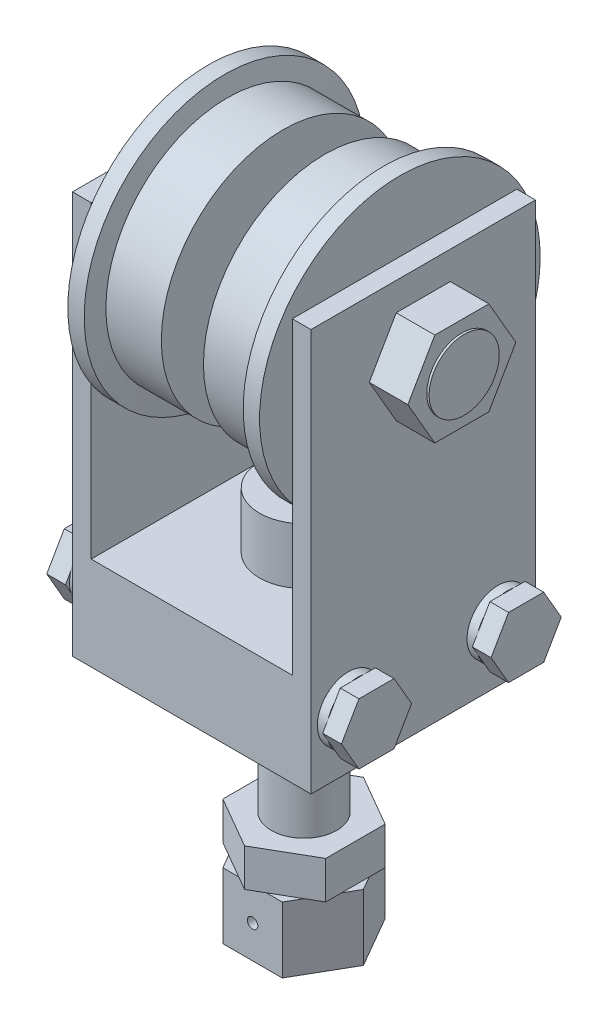
SolidWorks part; units mm, degrees
ref_plane "Front" through (0, 0, 0) normal (0, 0, 1) x (1, 0, 0)
ref_plane "Top" through (0, 0, 0) normal (0, 1, 0) x (1, 0, 0)
ref_plane "Right" through (0, 0, 0) normal (1, 0, 0) x (0, 0, -1)
ref_plane "Z PLANE" through (0, 0, 0) normal (0, 0, 1) x (1, 0, 0)
ref_plane "YOKE BOTTOM" through (0, 0, 0) normal (0, 1, 0) x (-1, 0, 0)
ref_plane "X PLANE" through (0, 0, 0) normal (1, 0, 0) x (0, 0, -1)
sketch "YOKE CROSS SECTION" plane through (0, 0, 0) normal (1, 0, 0) x (0, 0, -1)
  line L0 (0, 0) -> (0, 57.0916) construction
  line L1 (0, 84.8167) -> (0, -84.8167) construction
  line L2 (-76.2, 0) -> (76.2, 0)
  line L3 (69.1602, 0) -> (-69.1602, 0) construction
  line L4 (76.2, 0) -> (76.2, 63.5)
  line L5 (-76.2, 0) -> (-76.2, 63.5)
  line L6 (76.2, 63.5) -> (-76.2, 63.5)
  point P12 (0, 63.5)
  dimension "D1" = 63.5
  dimension "D2" = 152.4
ref_plane "1/2 YOKE LENGTH (A)" through (68.2625, 0, 0) normal (1, 0, 0) x (0, 0, -1)
extrude "YOKE" add sketch "YOKE CROSS SECTION" along normal up to surface (68.2625 mm away) up to plane "1/2 YOKE LENGTH (A)"
sketch "SIDEPLATE PROFILE" plane through (68.2625, 0, 0) normal (1, 0, 0) x (0, 0, -1)
  line L0 (0, 0) -> (0, 74.7424) construction
  line L1 (0, 84.8167) -> (0, -84.8167) construction
  line L2 (-76.2, 0) -> (76.2, 0)
  line L3 (76.2, 0) -> (76.2, 273.05)
  line L4 (-76.2, 0) -> (-76.2, 273.05)
  line L5 (76.2, 273.05) -> (-76.2, 273.05)
  point P11 (0, 273.05)
  dimension "D1" = 273.05
ref_plane "WHEEL HEIGHT" through (0, 222.25, 0) normal (0, 1, 0) x (-1, 0, 0)
ref_plane "SCREW LOCATION X" through (0, 0, 50.8) normal (0, 0, 1) x (1, 0, 0)
ref_plane "SCREW LOCATION Y" through (0, 38.1, 0) normal (0, 1, 0) x (-1, 0, 0)
extrude "SIDEPLATE" add sketch "SIDEPLATE PROFILE" along normal blind 12.7
sketch "WHEEL PIN NUT PROFILE" plane through (80.9625, 0, 0) normal (1, 0, 0) x (0, 0, -1)
  line L0 (0, 84.8167) -> (0, -84.8167) construction
  line L1 (36.6617, 222.25) -> (18.3309, 254)
  line L2 (18.3309, 254) -> (-18.3309, 254)
  line L3 (-18.3309, 254) -> (-36.6617, 222.25)
  line L4 (-36.6617, 222.25) -> (-18.3309, 190.5)
  line L5 (-18.3309, 190.5) -> (18.3309, 190.5)
  line L6 (18.3309, 190.5) -> (36.6617, 222.25)
  line L7 (69.1602, 222.25) -> (-69.1602, 222.25) construction
  circle A0 centre (0, 222.25) radius 31.75 construction
  dimension "D1" = 63.5
extrude "WHEEL PIN NUT" add sketch "WHEEL PIN NUT PROFILE" along normal blind 26.1937
sketch "WHEEL PIN PROJECTION PROFILE" plane through (107.1563, 0, 0) normal (1, 0, 0) x (0, 0, -1)
  line L0 (0, 84.8167) -> (0, -84.8167) construction
  line L1 (69.1602, 222.25) -> (-69.1602, 222.25) construction
  circle A0 centre (0, 222.25) radius 23.8125
  dimension "D1" = 47.625
extrude "WHEEL PIN PROJECTION" add sketch "WHEEL PIN PROJECTION PROFILE" along normal blind 1.5875
sketch "LOCKNUTS PROFILE" plane through (80.9625, 0, 0) normal (1, 0, 0) x (0, 0, -1)
  line L0 (-50.8, 84.8167) -> (-50.8, -84.8167) construction
  line L1 (50, 38.1) -> (-50, 38.1) construction
  circle A0 centre (-50.8, 38.1) radius 21.0947
  dimension "D1" = 42.1894
extrude "LOCKNUTS" add sketch "LOCKNUTS PROFILE" along normal blind 6.35
sketch "SCREWS PROFILE" plane through (87.3125, 0, 0) normal (1, 0, 0) x (0, 0, -1)
  line L0 (50, 38.1) -> (-50, 38.1) construction
  line L1 (-26.9699, 38.1) -> (-38.8849, 58.7375)
  line L2 (-38.8849, 58.7375) -> (-62.7151, 58.7375)
  line L3 (-62.7151, 58.7375) -> (-74.6301, 38.1)
  line L4 (-74.6301, 38.1) -> (-62.7151, 17.4625)
  line L5 (-62.7151, 17.4625) -> (-38.8849, 17.4625)
  line L6 (-38.8849, 17.4625) -> (-26.9699, 38.1)
  line L7 (-50.8, 84.8167) -> (-50.8, -84.8167) construction
  circle A0 centre (-50.8, 38.1) radius 20.6375 construction
  dimension "D1" = 41.275
extrude "SCREWS" add sketch "SCREWS PROFILE" along normal blind 12.7
sketch "PROFILE" plane through (0, 63.5, 0) normal (0, 1, 0) x (-1, 0, 0)
  line L0 (84.8167, 0) -> (-84.8167, 0) construction
  line L1 (0, 83.2389) -> (0, -83.2389) construction
  circle A0 centre (0, 0) radius 30.1625
  dimension "D1" = 60.325
extrude "KING BOLT HEAD" add sketch "PROFILE" along normal blind 38.1
mirror "Mirror1" about plane through (0, 0, 0) normal (0, 0, 1) of "SCREWS", "LOCKNUTS"
mirror "Mirror5" about plane through (0, 0, 0) normal (1, 0, 0) of bodies 112
ref_plane "TOP OF NUT" through (0, -88.9, 0) normal (0, 1, 0) x (-1, 0, 0)
sketch "DIA." plane through (0, 0, 0) normal (0, -1, 0) x (1, 0, 0)
  line L0 (84.8167, 0) -> (-84.8167, 0) construction
  line L1 (0, -83.2389) -> (0, 83.2389) construction
  circle A0 centre (0, 0) radius 22.225
  dimension "D1" = 44.45
extrude "KING BOLT" add sketch "DIA." along normal up to surface (88.9 mm away) up to plane "TOP OF NUT"
sketch "KING BOLT JAN NUT PROFILE" plane through (0, -88.9, 0) normal (0, -1, 0) x (1, 0, 0)
  line L0 (84.8167, 0) -> (-84.8167, 0) construction
  line L1 (0, -40.3279) -> (34.925, -20.164)
  line L2 (34.925, -20.164) -> (34.925, 20.164)
  line L3 (34.925, 20.164) -> (0, 40.3279)
  line L4 (0, 40.3279) -> (-34.925, 20.164)
  line L5 (-34.925, 20.164) -> (-34.925, -20.164)
  line L6 (-34.925, -20.164) -> (0, -40.3279)
  line L7 (0, -83.2389) -> (0, 83.2389) construction
  circle A0 centre (0, 0) radius 34.925 construction
  dimension "D1" = 69.85
extrude "KING BOLT JAM NUT" add sketch "KING BOLT JAN NUT PROFILE" along normal blind 25.6286
sketch "KING BOLT NUT PROFILE" plane through (0, -114.5286, 0) normal (0, -1, 0) x (1, 0, 0)
  line L1 (40.3279, 0) -> (20.164, 34.925)
  line L2 (20.164, 34.925) -> (-20.164, 34.925)
  line L3 (-20.164, 34.925) -> (-40.3279, 0)
  line L4 (-40.3279, 0) -> (-20.164, -34.925)
  line L5 (-20.164, -34.925) -> (20.164, -34.925)
  line L6 (20.164, -34.925) -> (40.3279, 0)
  line L10 (0, -83.2389) -> (0, 83.2389) construction
  line L11 (84.8167, 0) -> (-84.8167, 0) construction
  circle A0 centre (0, 0) radius 34.925 construction
  dimension "D1" = 69.85
extrude "KING BOLT NUT" add sketch "KING BOLT NUT PROFILE" along normal blind 44.6786
sketch "Sketch5" plane through (0, -159.2072, 0) normal (0, -1, 0) x (1, 0, 0)
  circle A0 centre (0, 0) radius 22.225 construction
  circle A1 centre (0, 0) radius 22.225
extrude "EXTENDED KING BOLT" add sketch "Sketch5" along normal blind 9.525
chamfer "Chamfer1" distance 2.3812 angle 45 1 edges at (0, -168.7322, -22.225)
ref_plane "MOUNTING REF PLANE" through (0, -34.925, 0) normal (0, 1, 0) x (-1, 0, 0)
sketch "Sketch6" plane through (0, 0, 0) normal (0, 0, 1) x (1, 0, 0)
  line L0 (68.2625, 254) -> (68.2625, 222.25)
  line L1 (68.2625, 222.25) -> (68.2625, 254)
  line L2 (14.2875, 222.25) -> (14.2875, 304.8)
  line L3 (68.2625, 222.25) -> (14.2875, 222.25)
  line L4 (51.9635, 304.8) -> (53.975, 317.5)
  line L5 (65.0875, 254) -> (65.0875, 317.5)
  line L6 (65.0875, 254) -> (68.2625, 254)
  line L7 (53.975, 317.5) -> (65.0875, 317.5)
  line L8 (69.1602, 222.25) -> (-69.1602, 222.25) construction
  line L9 (51.9635, 304.8) -> (14.2875, 304.8)
  line L11 (68.2625, -75.0522) -> (68.2625, 75.0522) construction
  dimension "D1" = 31.75
  dimension "D2" = 63.5
  dimension "D3" = 53.975
  dimension "D4" = 82.55
  dimension "D5" = 11.1125
  dimension "D6" = 3.175
  dimension "D10" = 12.8583
revolve "WHEEL" add sketch "Sketch6" angle 360 about L3
mirror "Mirror6" about plane through (0, 0, 0) normal (1, 0, 0) of "WHEEL"
sketch "Sketch7" plane through (0, 0, 34.925) normal (0, 0, 1) x (1, 0, 0)
  line L0 (0, -83.2389) -> (0, 83.2389) construction
  line L1 (-20.164, -159.2072) -> (-40.3279, -159.2072) construction
  circle A0 centre (0, -136.9822) radius 3.5719
  dimension "D2" = 7.1437
  dimension "D1" = 22.225
extrude "COTTER PIN HOLE" cut sketch "Sketch7" against normal up to next
sketch "Sketch8" plane through (0, 0, 0) normal (0, -1, 0) x (1, 0, 0)
  circle A0 centre (0, 0) radius 25.4
  circle A1 centre (0, 0) radius 30.1625
  dimension "D1" = 50.8
  dimension "D2" = 60.325
extrude "SPACER" add sketch "Sketch8" along normal blind 12.7
ref_plane "TREAD OF TRACK" through (0, 139.7, 0) normal (0, 1, 0) x (-1, 0, 0)
